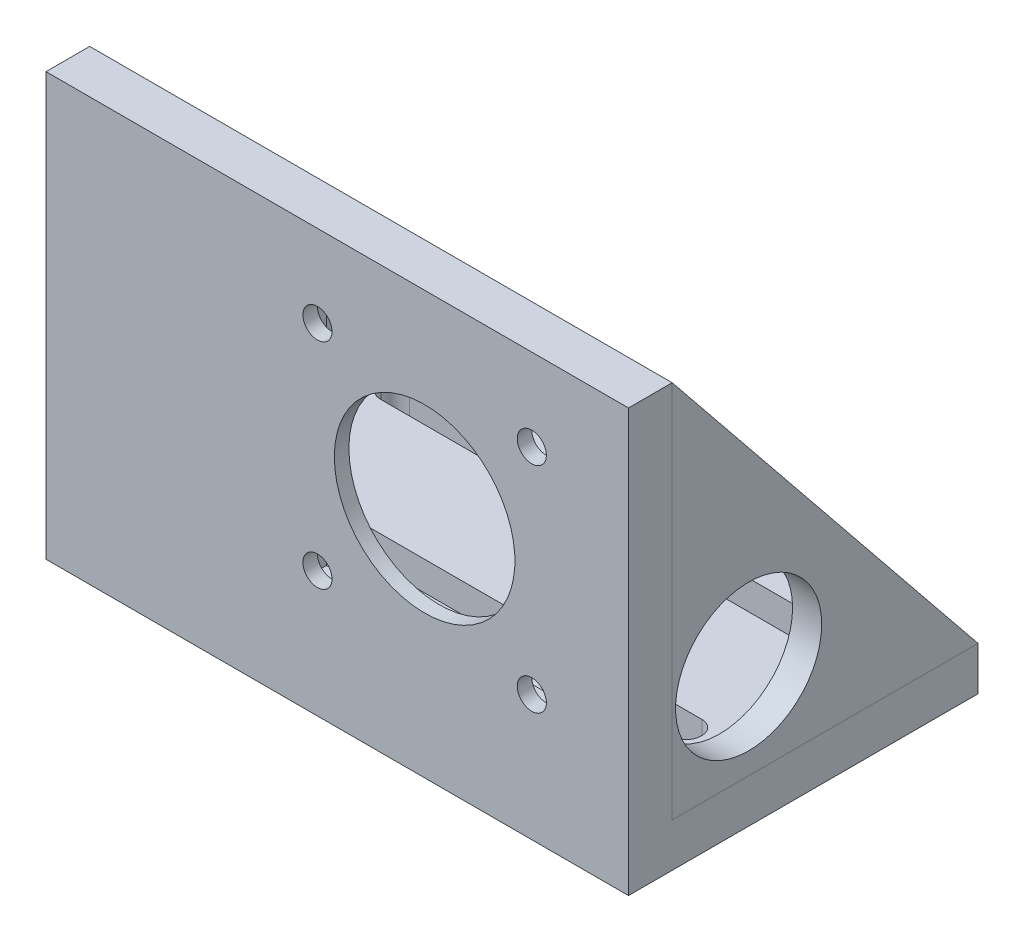
SolidWorks part; units mm, degrees
ref_plane "Front Plane" through (0, 0, 0) normal (0, 0, 1) x (1, 0, 0)
ref_plane "Top Plane" through (0, 0, 0) normal (0, 1, 0) x (1, 0, 0)
ref_plane "Right Plane" through (0, 0, 0) normal (1, 0, 0) x (0, 0, -1)
sketch "Sketch2" plane through (0, 0, 0) normal (0, 1, 0) x (1, 0, 0)
  line L1 (0, 0) -> (127, 0)
  line L2 (0, 0) -> (0, 76.2)
  line L3 (0, 76.2) -> (127, 76.2)
  line L4 (127, 0) -> (127, 76.2)
  dimension "D1" = 76.2
  dimension "D2" = 127
extrude "Boss-Extrude1" add sketch "Sketch2" along normal blind 9.525
sketch "Sketch3" plane through (0, 9.525, 0) normal (0, 1, 0) x (1, 0, 0)
  line L0 (127, 0) -> (127, 76.2) construction
  line L1 (0, 0) -> (127, 0)
  line L2 (0, 0) -> (0, 9.525)
  line L3 (0, 9.525) -> (127, 9.525)
  line L4 (127, 0) -> (127, 9.525)
  dimension "D1" = 9.525
extrude "Boss-Extrude2" add sketch "Sketch3" along normal blind 82.55
sketch "Sketch4" plane through (127, 0, 0) normal (1, 0, 0) x (0, 0, -1)
  line L0 (9.525, 92.075) -> (76.2, 9.525)
  line L1 (76.2, 9.525) -> (9.525, 9.525)
  line L2 (9.525, 9.525) -> (9.525, 92.075)
extrude "Boss-Extrude3" add sketch "Sketch4" against normal blind 6.35 separate body
sketch "Sketch5" plane through (0, 0, 0) normal (-1, 0, 0) x (0, 0, 1)
  line L0 (-9.525, 92.075) -> (-76.2, 9.525)
  line L1 (-76.2, 9.525) -> (-9.525, 9.525)
  line L2 (-9.525, 9.525) -> (-9.525, 92.075)
extrude "Boss-Extrude4" add sketch "Sketch5" against normal blind 6.35
sketch "Sketch7" plane through (0, 0, -9.525) normal (0, 0, -1) x (-1, 0, 0)
  line L0 (-82.55, 92.075) -> (-82.55, 9.525) construction
  line L1 (-120.65, 9.525) -> (-120.65, 92.075) construction
  line L3 (-82.55, 50.8) -> (-39.9433, 50.8) construction
  circle A0 centre (-82.55, 50.8) radius 19.685
  circle A2 centre (-105.918, 74.168) radius 3.175
  circle A3 centre (-59.182, 74.168) radius 3.175
  circle A6 centre (-59.182, 27.432) radius 3.175
  circle A7 centre (-105.918, 27.432) radius 3.175
  dimension "D1" = 23.368
  dimension "D5" = 38.1
  dimension "D2" = 23.368
  dimension "D3" = 23.368
  dimension "D4" = 23.368
extrude "Cut-Extrude1" cut sketch "Sketch7" against normal through all
sketch "Sketch11" plane through (0, 0, -9.525) normal (0, 0, -1) x (-1, 0, 0)
  line L1 (-113.5107, 81.7423) -> (-51.5893, 81.7423)
  line L2 (-113.5107, 81.7423) -> (-113.5107, 19.8577)
  line L3 (-113.5107, 19.8577) -> (-51.5893, 19.8577)
  line L4 (-51.5893, 81.7423) -> (-51.5893, 19.8577)
  line L5 (-113.5107, 81.7423) -> (-51.5893, 19.8577) construction
  line L6 (-113.5107, 19.8577) -> (-51.5893, 81.7423) construction
  point P0 (-82.55, 50.8)
extrude "Cut-Extrude4" cut sketch "Sketch11" against normal blind 6.35
sketch "Sketch12" plane through (0, 0, 0) normal (0, -1, 0) x (1, 0, 0)
  line L0 (0, -76.2) -> (0, 0) construction
  line L1 (15.748, -63.5) -> (111.252, -63.5)
  line L2 (12.7, -60.452) -> (12.7, -60.198)
  line L3 (15.748, -57.15) -> (111.252, -57.15)
  line L4 (114.3, -60.452) -> (114.3, -60.198)
  line L5 (127, -76.2) -> (0, -76.2) construction
  line L6 (15.748, -25.4) -> (111.252, -25.4)
  line L7 (15.748, -31.75) -> (111.252, -31.75)
  line L8 (114.3, -28.702) -> (114.3, -28.448)
  line L9 (12.7, -28.702) -> (12.7, -28.448)
  arc A0 (111.252, -63.5) -> (114.3, -60.452) centre (111.252, -60.452) ccw
  arc A1 (114.3, -60.198) -> (111.252, -57.15) centre (111.252, -60.198) ccw
  arc A2 (15.748, -57.15) -> (12.7, -60.198) centre (15.748, -60.198) ccw
  arc A3 (12.7, -60.452) -> (15.748, -63.5) centre (15.748, -60.452) ccw
  arc A4 (114.3, -28.448) -> (111.252, -25.4) centre (111.252, -28.448) ccw
  arc A5 (111.252, -31.75) -> (114.3, -28.702) centre (111.252, -28.702) ccw
  arc A6 (12.7, -28.702) -> (15.748, -31.75) centre (15.748, -28.702) ccw
  arc A7 (15.748, -25.4) -> (12.7, -28.448) centre (15.748, -28.448) ccw
  point P10 (114.3, -63.5)
  point P15 (12.7, -57.15)
  point P18 (12.7, -63.5)
  dimension "D5" = 3.048
  dimension "D1" = 101.6
  dimension "D2" = 6.35
  dimension "D3" = 12.7
  dimension "D4" = 12.7
  dimension "D6" = 2
extrude "Cut-Extrude5" cut sketch "Sketch12" against normal through all
sketch "Sketch13" plane through (6.35, 0, 0) normal (1, 0, 0) x (0, 0, -1)
  line L0 (9.525, 9.525) -> (42.8625, 50.8) construction
  line L1 (9.525, 92.075) -> (76.2, 9.525) construction
  circle A0 centre (26.1938, 30.1625) radius 15.9292
extrude "Cut-Extrude6" cut sketch "Sketch13" against normal through all both and the other way through all
